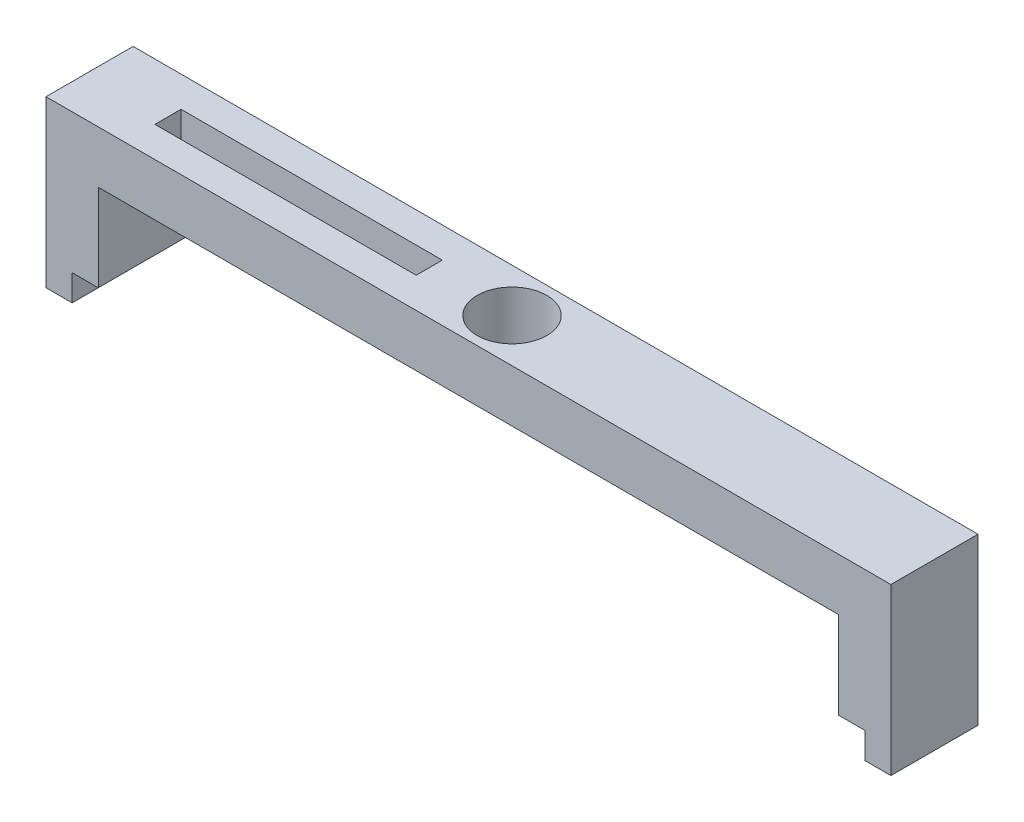
SolidWorks part; units mm, degrees
ref_plane "Alzado" through (0, 0, 0) normal (0, 0, 1) x (1, 0, 0)
ref_plane "Planta" through (0, 0, 0) normal (0, 1, 0) x (1, 0, 0)
ref_plane "Vista lateral" through (0, 0, 0) normal (1, 0, 0) x (0, 0, -1)
sketch "Croquis2" plane through (0, 0, 0) normal (0, 0, 1) x (1, 0, 0)
  line L0 (-43.4121, 0) -> (35.5879, 0)
  line L5 (41.5879, -10) -> (41.5879, -13)
  line L6 (41.5879, -13) -> (44.5879, -13)
  line L7 (44.5879, -13) -> (44.5879, 6)
  line L8 (44.5879, 6) -> (-52.4121, 6)
  line L9 (-52.4121, 6) -> (-52.4121, -13)
  line L10 (-52.4121, -13) -> (-49.4121, -13)
  line L11 (-49.4121, -13) -> (-49.4121, -10)
  line L16 (-49.4121, -10) -> (-46.4121, -10)
  line L17 (38.5879, -10) -> (41.5879, -10)
  line L18 (38.5879, -10) -> (38.5879, 0)
  line L19 (38.5879, 0) -> (35.5879, 0)
  line L20 (-46.4121, -10) -> (-46.4121, 0)
  line L21 (-46.4121, 0) -> (-43.4121, 0)
  dimension "D1" = 79
  dimension "D3" = 10
  dimension "D6" = 3
  dimension "D7" = 3
  dimension "D9" = 13
  dimension "D11" = 13
  dimension "D12" = 6
  dimension "10" = 10
extrude "Saliente-Extruir1" add sketch "Croquis2" along normal blind 10
sketch "Croquis3" plane through (0, 0, 0) normal (0, 1, 0) x (1, 0, 0)
  line L0 (-52.4121, 0) -> (44.5879, -10) construction
  line L1 (44.5879, 0) -> (-52.4121, -10) construction
  line L3 (-43.4121, -6.5) -> (-13.4121, -6.5)
  line L4 (-43.4121, -6.5) -> (-43.4121, -3.5)
  line L5 (-43.4121, -3.5) -> (-13.4121, -3.5)
  line L6 (-13.4121, -6.5) -> (-13.4121, -3.5)
  line L7 (-43.4121, -6.5) -> (-13.4121, -3.5) construction
  line L8 (-43.4121, -3.5) -> (-13.4121, -6.5) construction
  circle A0 centre (-3.9121, -5) radius 4
  point P10 (-28.4121, -5)
  dimension "D1" = 8
  dimension "D2" = 9.5
  dimension "D3" = 30
  dimension "D4" = 3
sketch "Croquis4" plane through (0, 6, 0) normal (0, 1, 0) x (1, 0, 0)
  line L1 (-43.4121, -6.5) -> (-13.4121, -6.5)
  line L2 (-43.4121, -6.5) -> (-43.4121, -3.5)
  line L3 (-43.4121, -3.5) -> (-13.4121, -3.5)
  line L4 (-13.4121, -6.5) -> (-13.4121, -3.5)
  line L5 (-43.4121, -6.5) -> (-13.4121, -3.5) construction
  line L6 (-43.4121, -3.5) -> (-13.4121, -6.5) construction
  circle A0 centre (-3.9121, -5) radius 4
  point P3 (-28.4121, -5)
extrude "Cortar-Extruir1" cut sketch "Croquis4" against normal blind 10
